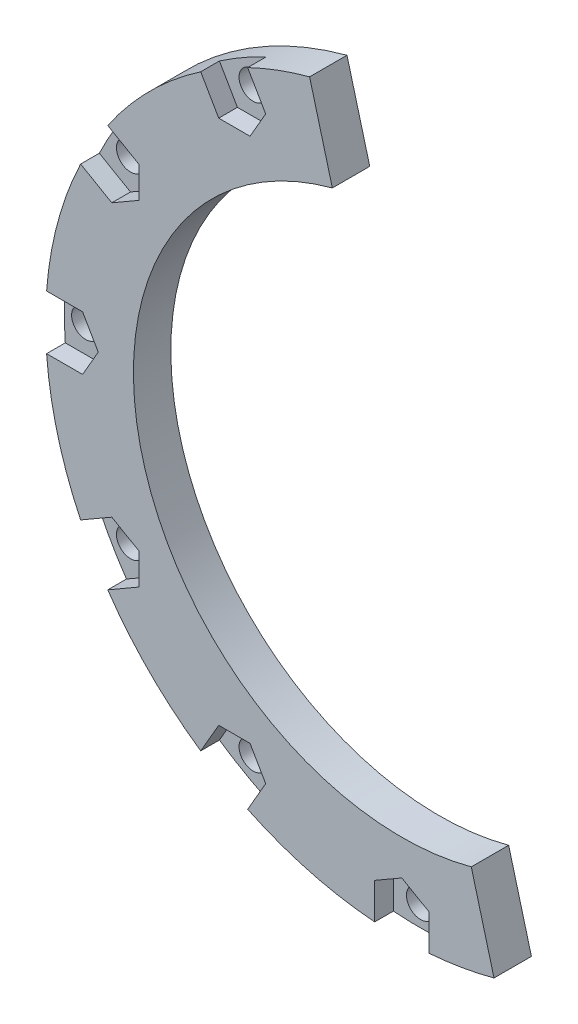
SolidWorks part; units mm, degrees
ref_plane "Front Plane" through (0, 0, 0) normal (0, 0, 1) x (1, 0, 0)
ref_plane "Top Plane" through (0, 0, 0) normal (0, 1, 0) x (1, 0, 0)
ref_plane "Right Plane" through (0, 0, 0) normal (1, 0, 0) x (0, 0, -1)
sketch "Sketch1" plane through (0, 0, 0) normal (0, 0, 1) x (1, 0, 0)
  circle A0 centre (0, 0) radius 38.1
  circle A1 centre (0, 0) radius 28.702
  dimension "D1" = 76.2
  dimension "D2" = 57.404
extrude "Boss-Extrude1" add sketch "Sketch1" along normal blind 4
sketch "Sketch2" plane through (0, 0, 4) normal (0, 0, 1) x (1, 0, 0)
  line L0 (0, 0) -> (0, 44.3901) construction
  circle A0 centre (0, 0) radius 35.814 construction
  circle A1 centre (0, 35.814) radius 1.5
  circle A2 centre (17.907, 31.0158) radius 1.5
  circle A3 centre (31.0158, 17.907) radius 1.5
  circle A4 centre (35.814, 0) radius 1.5
  circle A5 centre (31.0158, -17.907) radius 1.5
  circle A6 centre (17.907, -31.0158) radius 1.5
  circle A7 centre (0, -35.814) radius 1.5
  circle A8 centre (-17.907, -31.0158) radius 1.5
  circle A9 centre (-31.0158, -17.907) radius 1.5
  circle A10 centre (-35.814, 0) radius 1.5
  circle A11 centre (-31.0158, 17.907) radius 1.5
  circle A12 centre (-17.907, 31.0158) radius 1.5
  point P30 (0, 0)
  dimension "D1" = 71.628
  dimension "D2" = 3
  dimension "D3" = 12
extrude "Cut-Extrude1" cut sketch "Sketch2" against normal through all
sketch "Sketch3" plane through (0, 0, 4) normal (0, 0, 1) x (1, 0, 0)
  line L0 (0, 0) -> (0, 45.6158) construction
  line L1 (-2.9, 37.9895) -> (0, 39.1626)
  line L2 (16.4833, 34.3498) -> (19.5813, 33.9158)
  line L3 (-2.9, 37.9895) -> (-2.9, 34.1397)
  line L4 (-2.9, 34.1397) -> (0, 32.4654)
  line L5 (0, 32.4654) -> (2.9, 34.1397)
  line L6 (2.9, 34.1397) -> (2.9, 37.9895)
  line L7 (16.4833, 34.3498) -> (14.5584, 31.0158)
  line L8 (2.9, 37.9895) -> (0, 39.1626)
  line L9 (14.5584, 31.0158) -> (16.2327, 28.1158)
  line L10 (16.2327, 28.1158) -> (19.5813, 28.1158)
  line L11 (19.5813, 28.1158) -> (21.5062, 31.4498)
  line L12 (21.5062, 31.4498) -> (19.5813, 33.9158)
  line L13 (31.4498, 21.5062) -> (33.9158, 19.5813)
  line L14 (31.4498, 21.5062) -> (28.1158, 19.5813)
  line L15 (28.1158, 19.5813) -> (28.1158, 16.2327)
  line L16 (28.1158, 16.2327) -> (31.0158, 14.5584)
  line L17 (31.0158, 14.5584) -> (34.3498, 16.4833)
  line L18 (34.3498, 16.4833) -> (33.9158, 19.5813)
  line L19 (37.9895, 2.9) -> (39.1626, 0)
  line L20 (37.9895, 2.9) -> (34.1397, 2.9)
  line L21 (34.1397, 2.9) -> (32.4654, 0)
  line L22 (32.4654, 0) -> (34.1397, -2.9)
  line L23 (34.1397, -2.9) -> (37.9895, -2.9)
  line L24 (37.9895, -2.9) -> (39.1626, 0)
  line L25 (34.3498, -16.4833) -> (33.9158, -19.5813)
  line L26 (34.3498, -16.4833) -> (31.0158, -14.5584)
  line L27 (31.0158, -14.5584) -> (28.1158, -16.2327)
  line L28 (28.1158, -16.2327) -> (28.1158, -19.5813)
  line L29 (28.1158, -19.5813) -> (31.4498, -21.5062)
  line L30 (31.4498, -21.5062) -> (33.9158, -19.5813)
  line L31 (21.5062, -31.4498) -> (19.5813, -33.9158)
  line L32 (21.5062, -31.4498) -> (19.5813, -28.1158)
  line L33 (19.5813, -28.1158) -> (16.2327, -28.1158)
  line L34 (16.2327, -28.1158) -> (14.5584, -31.0158)
  line L35 (14.5584, -31.0158) -> (16.4833, -34.3498)
  line L36 (16.4833, -34.3498) -> (19.5813, -33.9158)
  line L37 (2.9, -37.9895) -> (0, -39.1626)
  line L38 (2.9, -37.9895) -> (2.9, -34.1397)
  line L39 (2.9, -34.1397) -> (0, -32.4654)
  line L40 (0, -32.4654) -> (-2.9, -34.1397)
  line L41 (-2.9, -34.1397) -> (-2.9, -37.9895)
  line L42 (-2.9, -37.9895) -> (0, -39.1626)
  line L43 (-16.4833, -34.3498) -> (-19.5813, -33.9158)
  line L44 (-16.4833, -34.3498) -> (-14.5584, -31.0158)
  line L45 (-14.5584, -31.0158) -> (-16.2327, -28.1158)
  line L46 (-16.2327, -28.1158) -> (-19.5813, -28.1158)
  line L47 (-19.5813, -28.1158) -> (-21.5062, -31.4498)
  line L48 (-21.5062, -31.4498) -> (-19.5813, -33.9158)
  line L49 (-31.4498, -21.5062) -> (-33.9158, -19.5813)
  line L50 (-31.4498, -21.5062) -> (-28.1158, -19.5813)
  line L51 (-28.1158, -19.5813) -> (-28.1158, -16.2327)
  line L52 (-28.1158, -16.2327) -> (-31.0158, -14.5584)
  line L53 (-31.0158, -14.5584) -> (-34.3498, -16.4833)
  line L54 (-34.3498, -16.4833) -> (-33.9158, -19.5813)
  line L55 (-37.9895, -2.9) -> (-39.1626, 0)
  line L56 (-37.9895, -2.9) -> (-34.1397, -2.9)
  line L57 (-34.1397, -2.9) -> (-32.4654, 0)
  line L58 (-32.4654, 0) -> (-34.1397, 2.9)
  line L59 (-34.1397, 2.9) -> (-37.9895, 2.9)
  line L60 (-37.9895, 2.9) -> (-39.1626, 0)
  line L61 (-34.3498, 16.4833) -> (-33.9158, 19.5813)
  line L62 (-34.3498, 16.4833) -> (-31.0158, 14.5584)
  line L63 (-31.0158, 14.5584) -> (-28.1158, 16.2327)
  line L64 (-28.1158, 16.2327) -> (-28.1158, 19.5813)
  line L65 (-28.1158, 19.5813) -> (-31.4498, 21.5062)
  line L66 (-31.4498, 21.5062) -> (-33.9158, 19.5813)
  line L67 (-21.5062, 31.4498) -> (-19.5813, 33.9158)
  line L68 (-21.5062, 31.4498) -> (-19.5813, 28.1158)
  line L69 (-19.5813, 28.1158) -> (-16.2327, 28.1158)
  line L70 (-16.2327, 28.1158) -> (-14.5584, 31.0158)
  line L71 (-14.5584, 31.0158) -> (-16.4833, 34.3498)
  line L72 (-16.4833, 34.3498) -> (-19.5813, 33.9158)
  line L139 (0, 39.1626) -> (-1.45, 38.3255) [skipped]
  line L140 (2.9, 37.4883) -> (1.9248, 38.0513) [skipped]
  circle A0 centre (0, 35.814) radius 2.9 construction
  circle A1 centre (0, 0) radius 38.1 construction
  circle A2 centre (17.907, 31.0158) radius 2.9 construction
  circle A3 centre (31.0158, 17.907) radius 2.9 construction
  circle A4 centre (35.814, 0) radius 2.9 construction
  circle A5 centre (31.0158, -17.907) radius 2.9 construction
  circle A6 centre (17.907, -31.0158) radius 2.9 construction
  circle A7 centre (0, -35.814) radius 2.9 construction
  circle A8 centre (-17.907, -31.0158) radius 2.9 construction
  circle A9 centre (-31.0158, -17.907) radius 2.9 construction
  circle A10 centre (-35.814, 0) radius 2.9 construction
  circle A11 centre (-31.0158, 17.907) radius 2.9 construction
  circle A12 centre (-17.907, 31.0158) radius 2.9 construction
  point P103 (0, 0)
  point P105 (0, 0)
  dimension "D1" = 5.8
  dimension "D2" = 12
extrude "Cut-Extrude2" cut sketch "Sketch3" against normal blind 2
sketch "Sketch4" plane through (0, 0, 4) normal (0, 0, 1) x (1, 0, 0)
  line L0 (0, 0) -> (44.6741, 0) construction
  line L1 (-9.861, 36.8018) -> (9.861, -36.8018)
  arc A0 (-9.861, 36.8018) -> (9.861, -36.8018) centre (0, 0) cw
extrude "Cut-Extrude3" cut sketch "Sketch4" against normal through all both and the other way through all
